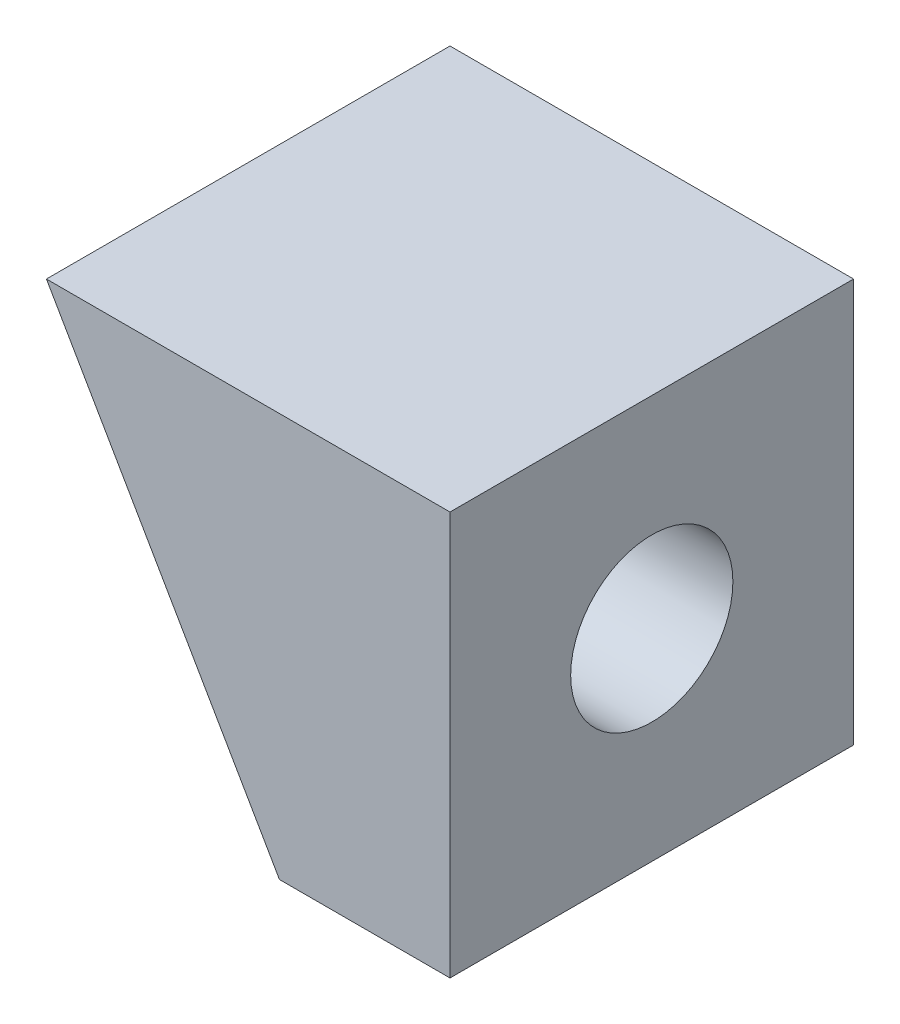
SolidWorks part; units mm, degrees
ref_plane "Front Plane" through (0, 0, 0) normal (0, 0, 1) x (1, 0, 0)
ref_plane "Top Plane" through (0, 0, 0) normal (0, 1, 0) x (1, 0, 0)
ref_plane "Right Plane" through (0, 0, 0) normal (1, 0, 0) x (0, 0, -1)
sketch "Sketch1" plane through (0, 0, 0) normal (1, 0, 0) x (0, 0, -1)
  line L1 (0, 0) -> (12.7, 0)
  line L2 (0, 0) -> (0, 12.7)
  line L3 (0, 12.7) -> (12.7, 12.7)
  line L4 (12.7, 0) -> (12.7, 12.7)
  dimension "D1" = 12.7
  dimension "D2" = 12.7
extrude "Boss-Extrude1" add sketch "Sketch1" along normal blind 12.7
sketch "Sketch2" plane through (0, 0, 0) normal (0, 0, 1) x (1, 0, 0)
  line L0 (0, 12.7) -> (7.3323, 0)
  line L6 (0, 12.7) -> (0, 0)
  line L7 (0, 0) -> (12.7, 0)
  line L8 (12.7, 0) -> (12.7, 12.7)
  line L9 (12.7, 12.7) -> (0, 12.7)
  line L10 (0, 12.7) -> (0, 0)
  line L11 (0, 0) -> (12.7, 0)
  line L12 (12.7, 0) -> (12.7, 12.7)
  line L13 (12.7, 12.7) -> (0, 12.7)
  line M7 (0, 12.7) -> (0, 0)
  line M8 (0, 0) -> (12.7, 0)
  dimension "D2" = 30
  dimension "D1" = 0
extrude "Cut-Extrude1" cut sketch "Sketch2" against normal through all contours L0 M7 M8
hole_wizard "#10 Clearance Hole1" positions "3DSketch1" profile "Sketch5" hole size "#10" standard "ANSI Inch" end condition through all
sketch3d "3DSketch1"
  line L0 (12.7, 12.7, -12.7) -> (12.7, 12.7, 0) construction
  line L1 (12.7, 0, -12.7) -> (12.7, 12.7, -12.7) construction
  point P0 (12.7, 6.35, -6.35)
  dimension "D1" = 6.35
  dimension "D2" = 6.35
sketch "Sketch5" plane through (12.7, 6.35, -6.35) normal (0, 1, 0) x (0, 0, -1)
  line L0 (0, 0) -> (0, 12.7)
  line L1 (0, 12.7) -> (2.5527, 12.7)
  line L2 (2.5527, 12.7) -> (2.5527, 0)
  line L5 (2.5527, 0) -> (0, 0)
  line L11 (0, -6.35) -> (0, 107.95) construction
  dimension "Thru Hole Dia." = 5.1054
  dimension "Thru Hole Depth" = 12.7
